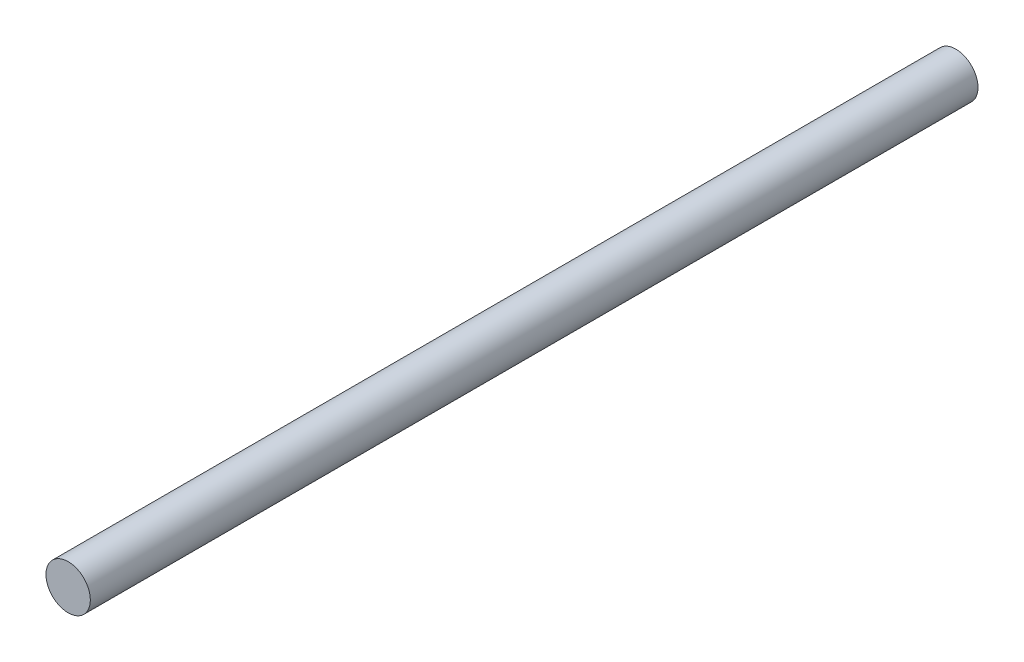
SolidWorks part; units mm, degrees
ref_plane "前视基准面" through (0, 0, 0) normal (0, 0, 1) x (1, 0, 0)
ref_plane "上视基准面" through (0, 0, 0) normal (0, 1, 0) x (1, 0, 0)
ref_plane "右视基准面" through (0, 0, 0) normal (1, 0, 0) x (0, 0, -1)
sketch "草图1" plane through (0, 0, 0) normal (0, 0, 1) x (1, 0, 0)
  circle A0 centre (0, 0) radius 4
  dimension "D1" = 8
extrude "凸台-拉伸1" add sketch "草图1" along normal blind 160
